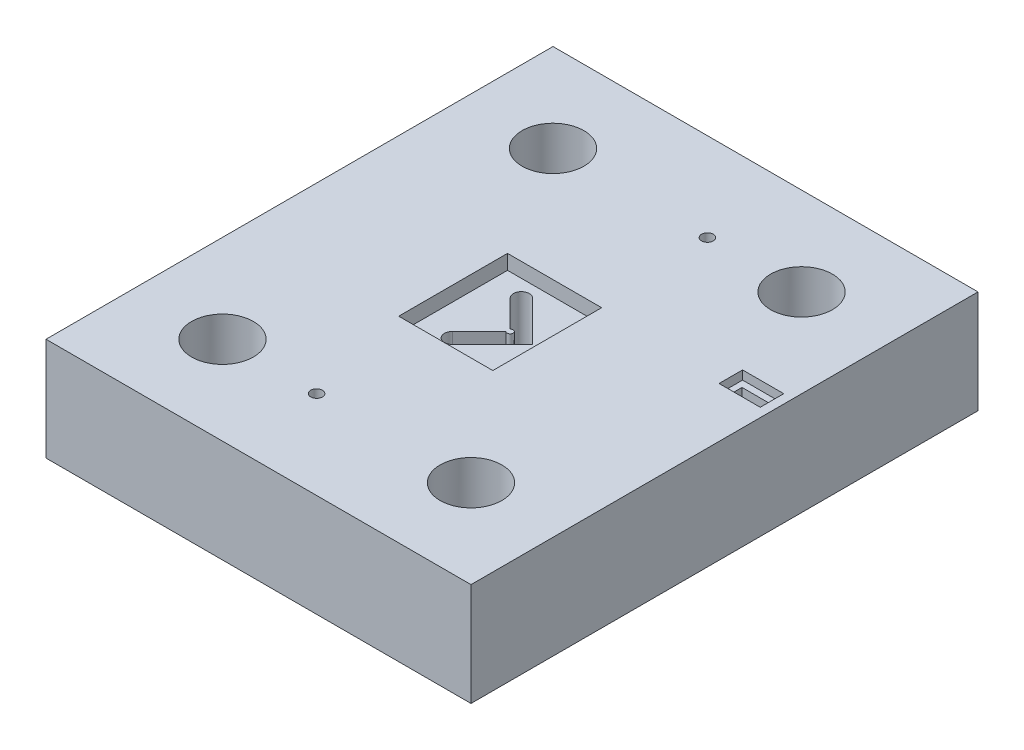
SolidWorks part; units mm, degrees
ref_plane "Front Plane" through (0, 0, 0) normal (0, 0, 1) x (1, 0, 0)
ref_plane "Top Plane" through (0, 0, 0) normal (0, 1, 0) x (1, 0, 0)
ref_plane "Right Plane" through (0, 0, 0) normal (1, 0, 0) x (0, 0, -1)
sketch "Sketch1" plane through (0, 0, 0) normal (0, 1, 0) x (1, 0, 0)
  line L1 (-72.25, -86.19) -> (72.25, -86.19)
  line L2 (-72.25, -86.19) -> (-72.25, 86.19)
  line L3 (-72.25, 86.19) -> (72.25, 86.19)
  line L4 (72.25, -86.19) -> (72.25, 86.19)
  line L5 (-72.25, -86.19) -> (72.25, 86.19) construction
  line L6 (-72.25, 86.19) -> (72.25, -86.19) construction
  point P0 (0, 0)
  dimension "D1" = 144.5
  dimension "D2" = 172.38
extrude "Boss-Extrude1" add sketch "Sketch1" along normal blind 35
sketch "Sketch6" plane through (0, 35, 0) normal (0, 1, 0) x (1, 0, 0)
  line L0 (72.25, 20.94) -> (57.25, 20.94) construction
  line L1 (67.25, 20.94) -> (67.25, 17.44) construction
  line L4 (65.25, 17.44) -> (65.25, 17.94) construction
  line L5 (67.25, 17.44) -> (65.25, 17.44) construction
  line L6 (-10.4555, 9.8288) -> (-1.3339, 0.7071)
  line L7 (7.01, 0) -> (-6.6372, 13.6472)
  line L8 (-6.6372, -13.6472) -> (7.01, 0)
  line L9 (-1.3339, -0.7071) -> (-10.4555, -9.8288)
  line L10 (-10.4555, 9.8288) -> (-1.3339, 0.7071)
  line L11 (7.01, 0) -> (-6.6372, 13.6472)
  line L12 (-6.6372, -13.6472) -> (7.01, 0)
  line L13 (-1.3339, -0.7071) -> (-10.4555, -9.8288)
  line L14 (59.25, 17.94) -> (59.25, 17.44) construction
  line L15 (57.25, 17.44) -> (57.25, 17.94) construction
  line L16 (59.25, 17.44) -> (57.25, 17.44) construction
  line L17 (57.25, 20.94) -> (57.25, 17.94) construction
  line L18 (65.25, 17.94) -> (59.25, 17.94) construction
  line L19 (67.25, 20.94) -> (67.25, 17.44)
  line L20 (65.25, 17.44) -> (65.25, 17.94)
  line L21 (67.25, 17.44) -> (65.25, 17.44)
  line L22 (59.25, 17.94) -> (59.25, 17.44)
  line L23 (57.25, 17.44) -> (57.25, 17.94)
  line L24 (59.25, 17.44) -> (57.25, 17.44)
  line L25 (57.25, 20.94) -> (57.25, 17.94)
  line L26 (67.25, 20.94) -> (57.25, 20.94)
  line L27 (65.25, 17.94) -> (59.25, 17.94)
  circle A0 centre (42.25, -56.19) radius 10.5 construction
  circle A1 centre (-10.25, -56.19) radius 1.99 construction
  circle A2 centre (-42.25, -56.19) radius 10.5 construction
  arc A3 (-1.3339, -0.7071) -> (-1.3339, 0.7071) centre (-0.6268, 0) ccw
  arc A4 (-6.6372, 13.6472) -> (-10.4555, 9.8288) centre (-8.5463, 11.738) ccw
  arc A5 (-10.4555, -9.8288) -> (-6.6372, -13.6472) centre (-8.5463, -11.738) ccw
  arc A6 (-1.3339, -0.7071) -> (-1.3339, 0.7071) centre (-0.6268, 0) ccw
  arc A7 (-6.6372, 13.6472) -> (-10.4555, 9.8288) centre (-8.5463, 11.738) ccw
  arc A8 (-10.4555, -9.8288) -> (-6.6372, -13.6472) centre (-8.5463, -11.738) ccw
  circle A9 centre (42.25, 56.19) radius 10.5 construction
  circle A10 centre (10.25, 56.19) radius 1.99 construction
  circle A11 centre (-42.25, 56.19) radius 10.5 construction
  circle A12 centre (42.25, -56.19) radius 10.5
  circle A13 centre (-10.25, -56.19) radius 1.99
  circle A14 centre (-42.25, -56.19) radius 10.5
  circle A15 centre (42.25, 56.19) radius 10.5
  circle A16 centre (10.25, 56.19) radius 1.99
  circle A17 centre (-42.25, 56.19) radius 10.5
  dimension "D1" = 0
extrude "Cut-Extrude1" cut sketch "Sketch6" against normal up to next
sketch "Sketch7" plane through (0, 35, 0) normal (0, 1, 0) x (1, 0, 0)
  line L9 (-19.0778, -19.4468) -> (12.9222, -19.4468)
  line L10 (12.9222, -19.4468) -> (12.9222, 17.5532)
  line L11 (12.9222, 17.5532) -> (-19.0778, 17.5532)
  line L12 (-19.0778, 17.5532) -> (-19.0778, -19.4468)
  line L13 (-19.0778, -19.4468) -> (12.9222, -19.4468)
  line L14 (12.9222, -19.4468) -> (12.9222, 17.5532)
  line L15 (12.9222, 17.5532) -> (-19.0778, 17.5532)
  line L16 (-19.0778, 17.5532) -> (-19.0778, -19.4468)
  dimension "D1" = 1
extrude "Cut-Extrude2" cut sketch "Sketch7" against normal blind 5
sketch "Sketch8" plane through (0, 35, 0) normal (0, 1, 0) x (1, 0, 0)
  line L9 (55.2, 23.2) -> (55.2, 15.2)
  line L10 (55.2, 15.2) -> (69.2, 15.2)
  line L11 (69.2, 15.2) -> (69.2, 23.2)
  line L12 (69.2, 23.2) -> (55.2, 23.2)
  line L13 (55.2, 23.2) -> (55.2, 15.2)
  line L14 (55.2, 15.2) -> (69.2, 15.2)
  line L15 (69.2, 15.2) -> (69.2, 23.2)
  line L16 (69.2, 23.2) -> (55.2, 23.2)
  dimension "D1" = 1
extrude "Cut-Extrude3" cut sketch "Sketch8" against normal blind 3
sketch "Sketch9" plane through (0, 0, 0) normal (0, -1, 0) x (1, 0, 0)
  circle A0 centre (42.25, -56.19) radius 15.25 construction
  circle A1 centre (-150, -137.51) radius 16 construction
  circle A2 centre (42.25, 56.19) radius 15.25 construction
  circle A3 centre (-42.25, 56.19) radius 15.25 construction
  circle A4 centre (42.25, -56.19) radius 15.25
  circle A5 centre (-150, -137.51) radius 16
  circle A6 centre (42.25, 56.19) radius 15.25
  circle A7 centre (-42.25, 56.19) radius 15.25
extrude "Cut-Extrude4" cut sketch "Sketch9" against normal blind 20
